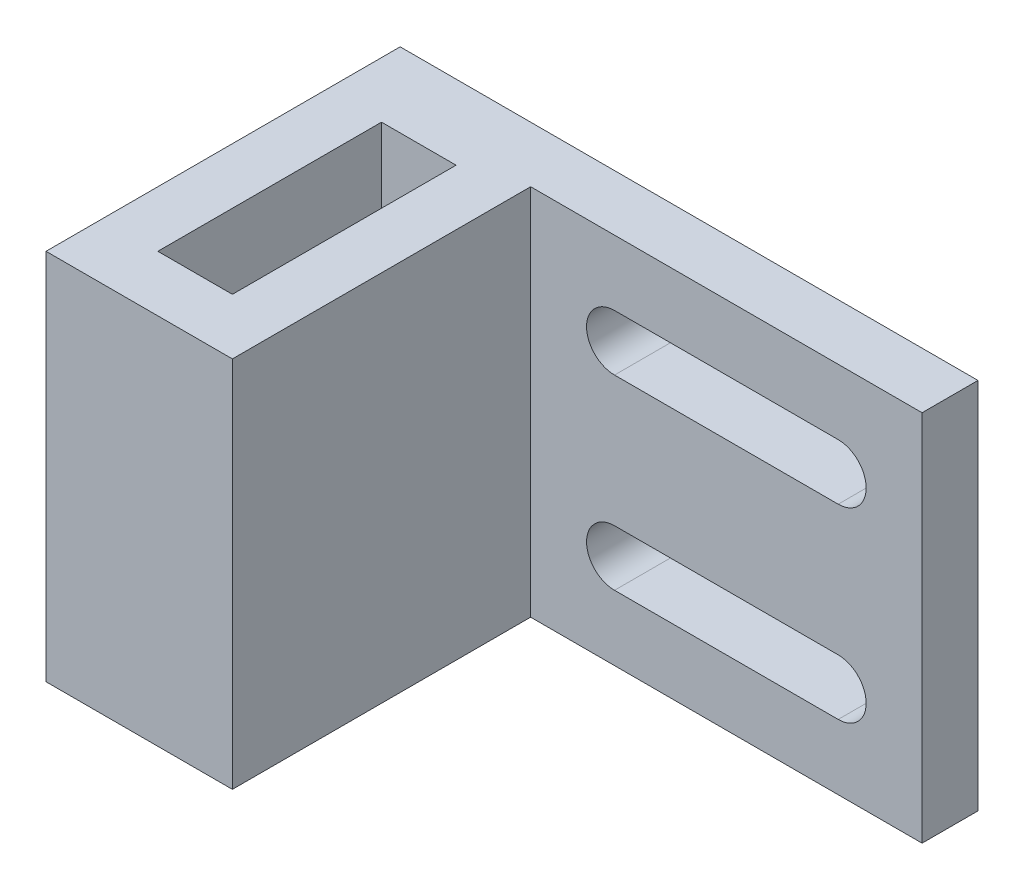
SolidWorks part; units mm, degrees
ref_plane "Front Plane" through (0, 0, 0) normal (0, 0, 1) x (1, 0, 0)
ref_plane "Top Plane" through (0, 0, 0) normal (0, 1, 0) x (1, 0, 0)
ref_plane "Right Plane" through (0, 0, 0) normal (1, 0, 0) x (0, 0, -1)
sketch "Croquis1" plane through (0, 0, 0) normal (0, 1, 0) x (1, 0, 0)
  line L0 (-5, 19) -> (-2, 19)
  line L1 (-2, 19) -> (-2, 3)
  line L2 (-2, 3) -> (2, 3)
  line L3 (2, 3) -> (2, 19)
  line L4 (2, 19) -> (26, 19)
  line L5 (26, 19) -> (26, 16)
  line L6 (26, 16) -> (5, 16)
  line L7 (5, 16) -> (5, 0)
  line L8 (5, 0) -> (-5, 0)
  line L9 (-5, 0) -> (-5, 19)
  point P2 (0, 0)
  dimension "D1" = 10
  dimension "D2" = 3
  dimension "D3" = 3
  dimension "D4" = 3
  dimension "D5" = 19
  dimension "D6" = 19
  dimension "D7" = 3
  dimension "D8" = 24
extrude "Saliente-Extruir1" add sketch "Croquis1" along normal blind 20
sketch "Croquis2" plane through (0, 0, -16) normal (0, 0, 1) x (1, 0, 0)
  line L0 (26, 10) -> (5, 10) construction
  line L1 (26, 20) -> (26, 0) construction
  line L2 (15.5, 20) -> (15.5, 10) construction
  line L3 (5, 20) -> (26, 20) construction
  line L4 (15.5, 15) -> (26, 15) construction
  line L5 (5, 20) -> (5, 0) construction
  line L6 (21.5, 16.5) -> (9.5, 16.5)
  line L7 (21.5, 13.5) -> (9.5, 13.5)
  line L8 (21.5, 3.5) -> (9.5, 3.5)
  line L9 (21.5, 6.5) -> (9.5, 6.5)
  arc A0 (21.5, 13.5) -> (21.5, 16.5) centre (21.5, 15) ccw
  arc A1 (9.5, 13.5) -> (9.5, 16.5) centre (9.5, 15) cw
  arc A2 (21.5, 6.5) -> (21.5, 3.5) centre (21.5, 5) cw
  arc A3 (9.5, 6.5) -> (9.5, 3.5) centre (9.5, 5) ccw
  point P15 (15.5, 13.5)
  point P20 (15.5, 16.5)
  dimension "D1" = 3
  dimension "D2" = 6
extrude "Cortar-Extruir1" cut sketch "Croquis2" against normal blind 20
sketch "Croquis3" plane through (-2, 0, 0) normal (1, 0, 0) x (0, 0, -1)
  line L0 (19, 20) -> (15, 20)
  line L1 (3, 20) -> (19, 20) construction
  line L2 (15, 20) -> (15, 0)
  line L3 (3, 0) -> (19, 0) construction
  line L4 (15, 0) -> (19, 0)
  line L5 (19, 0) -> (19, 20)
  dimension "D1" = 4
extrude "Saliente-Extruir2" add sketch "Croquis3" along normal blind 5
